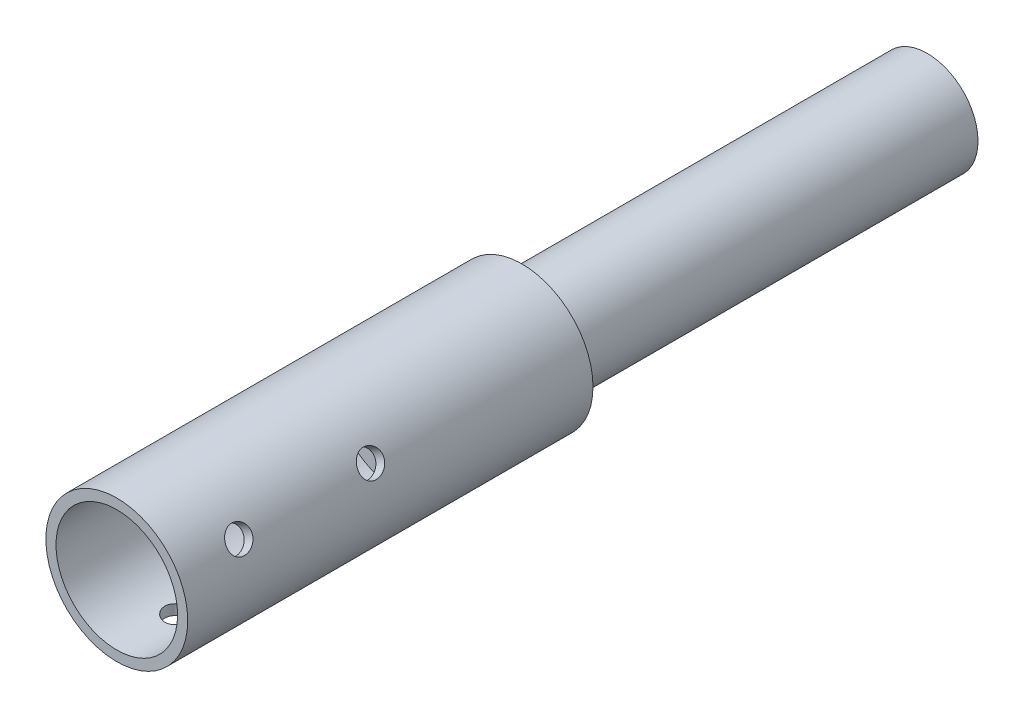
SolidWorks part; units mm, degrees
ref_plane "Alzado" through (0, 0, 0) normal (0, 0, 1) x (1, 0, 0)
ref_plane "Planta" through (0, 0, 0) normal (0, 1, 0) x (1, 0, 0)
ref_plane "Vista lateral" through (0, 0, 0) normal (1, 0, 0) x (0, 0, -1)
sketch "Croquis1" plane through (0, 0, 0) normal (1, 0, 0) x (0, 0, -1)
  line L0 (-95, 14) -> (-95, 12)
  line L1 (-95, 12) -> (-40, 12)
  line L2 (-40, 12) -> (-40, 0)
  line L3 (-40, 0) -> (65, 0)
  line L4 (65, 0) -> (65, 10)
  line L5 (65, 10) -> (-15, 10)
  line L6 (-15, 10) -> (-15, 14)
  line L7 (-15, 14) -> (-95, 14)
  line L8 (-144.0482, 0) -> (-104.7623, 0) construction
  point P11 (-40, 6)
  dimension "D1" = 20
  dimension "D2" = 28
  dimension "D3" = 80
  dimension "D4" = 24
  dimension "D5" = 55
  dimension "D6" = 160
  dimension "D7" = 40
revolve "Revolución1" add sketch "Croquis1" angle 360 about L8
sketch "Croquis2" plane through (0, 0, 0) normal (0, 1, 0) x (1, 0, 0)
  line L0 (-14, -95) -> (14, -95) construction
  circle A0 centre (0, -83) radius 2.5
  circle A1 centre (0, -57) radius 2.5
  dimension "D1" = 5
  dimension "D2" = 12
  dimension "D3" = 38
extrude "Cortar-Extruir1" cut sketch "Croquis2" against normal blind 15
ref_axis "Eje1" through (0, 0, 103) along (0, 0, -1)
pattern_circular "MatrizC1" count 3 over 360 about axis through (0, 0, 103) along (0, 0, -1) of "Cortar-Extruir1"
